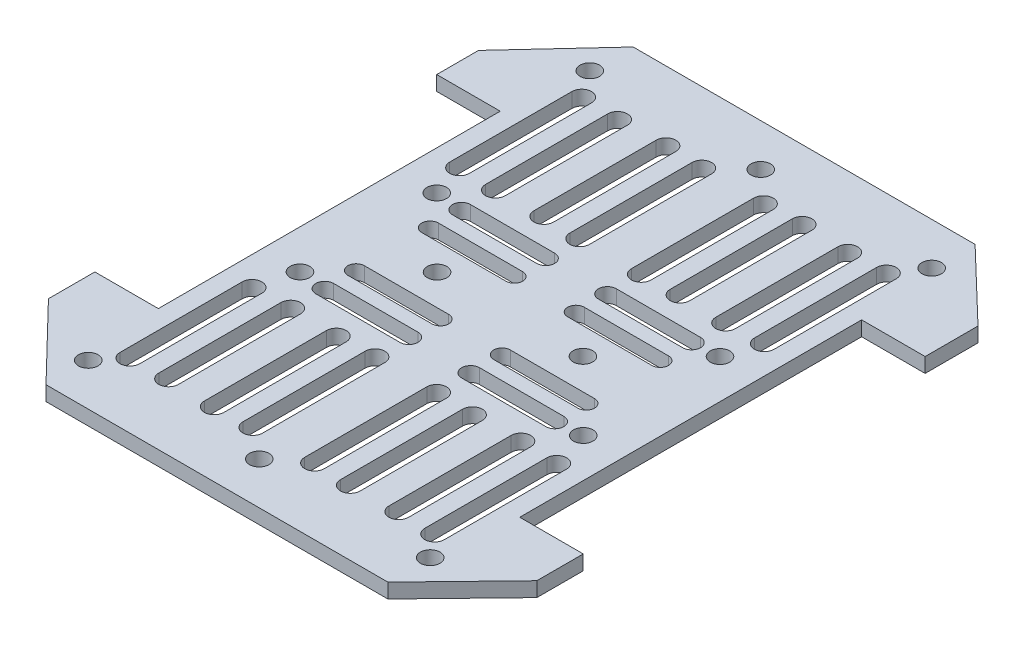
SolidWorks part; units mm, degrees
ref_plane "Front Plane" through (0, 0, 0) normal (0, 0, 1) x (1, 0, 0)
ref_plane "Top Plane" through (0, 0, 0) normal (0, 1, 0) x (1, 0, 0)
ref_plane "Right Plane" through (0, 0, 0) normal (1, 0, 0) x (0, 0, -1)
sketch "Sketch1" plane through (0, 0, 0) normal (0, 1, 0) x (1, 0, 0)
  line L0 (-79.583, 48.3629) -> (-79.583, 23.3559)
  line L1 (-83.6071, 48.3629) -> (-83.6071, 23.3559)
  line L2 (-71.9541, 48.0755) -> (-71.9541, 23.0685)
  line L3 (-73.9662, 14.2814) -> (-91.2181, 14.2814)
  line L4 (-75.9782, 48.0755) -> (-75.9782, 23.0685)
  line L5 (-96.8349, 48.3629) -> (-96.8349, 23.3559)
  line L6 (-100.859, 48.3629) -> (-100.859, 23.3559)
  line L7 (-89.206, 48.0755) -> (-89.206, 23.0685)
  line L8 (-93.2301, 48.0755) -> (-93.2301, 23.0685)
  line L9 (-55.7275, 48.3629) -> (-55.7275, 23.3559)
  line L10 (-51.7033, 48.3629) -> (-51.7033, 23.3559)
  line L11 (-63.3564, 48.0755) -> (-63.3564, 23.0685)
  line L12 (-59.3322, 48.0755) -> (-59.3322, 23.0685)
  line L13 (-38.4756, 48.3629) -> (-38.4756, 23.3559)
  line L14 (-34.4515, 48.3629) -> (-34.4515, 23.3559)
  line L15 (-46.1045, 48.0755) -> (-46.1045, 23.0685)
  line L16 (-42.0804, 48.0755) -> (-42.0804, 23.0685)
  line L17 (-117.7082, 46.1857) -> (-117.7082, 37.5391)
  line L18 (-79.583, -44.139) -> (-79.583, -19.132)
  line L19 (-83.6071, -44.139) -> (-83.6071, -19.132)
  line L20 (-71.9541, -43.8516) -> (-71.9541, -18.8446)
  line L21 (-75.9782, -43.8516) -> (-75.9782, -18.8446)
  line L22 (-96.8349, -44.139) -> (-96.8349, -19.132)
  line L23 (-100.859, -44.139) -> (-100.859, -19.132)
  line L24 (-89.206, -43.8516) -> (-89.206, -18.8446)
  line L25 (-93.2301, -43.8516) -> (-93.2301, -18.8446)
  line L26 (-55.7275, -44.139) -> (-55.7275, -19.132)
  line L27 (-51.7033, -44.139) -> (-51.7033, -19.132)
  line L28 (-63.3564, -43.8516) -> (-63.3564, -18.8446)
  line L29 (-59.3322, -43.8516) -> (-59.3322, -18.8446)
  line L30 (-32.7082, -57.4609) -> (-102.7082, -57.4609)
  line L31 (-117.7082, 46.1857) -> (-117.6732, 46.1313)
  line L32 (-32.4828, 62.5391) -> (-102.4828, 62.5391)
  line L33 (-102.4828, 62.5391) -> (-117.6732, 46.1313)
  line L34 (-102.7082, -57.4609) -> (-117.7082, -41.9617)
  line L36 (-117.7082, 37.5391) -> (-104.7082, 37.5391)
  line L37 (-117.7082, -32.4609) -> (-104.7082, -32.4609)
  line L38 (-104.7082, 37.5391) -> (-104.7082, -32.4609)
  line L39 (-38.4756, -44.139) -> (-38.4756, -19.132)
  line L40 (-117.7082, -32.4609) -> (-117.7082, -41.9617)
  line L41 (-34.4515, -44.139) -> (-34.4515, -19.132)
  line L42 (-46.1045, -43.8516) -> (-46.1045, -18.8446)
  line L43 (-42.0804, -43.8516) -> (-42.0804, -18.8446)
  line L44 (-73.9662, 17.9425) -> (-91.2181, 17.9425)
  line L45 (-73.9662, 7.9844) -> (-91.2181, 7.9844)
  line L46 (-73.9662, 11.3858) -> (-91.2181, 11.3858)
  line L47 (-61.3443, 14.2814) -> (-44.0924, 14.2814)
  line L48 (-61.3443, 17.9425) -> (-44.0924, 17.9425)
  line L49 (-61.3443, 7.9844) -> (-44.0924, 7.9844)
  line L50 (-61.3443, 11.3858) -> (-44.0924, 11.3858)
  line L51 (-73.9662, -10.0575) -> (-91.2181, -10.0575)
  line L52 (-73.9662, -13.7186) -> (-91.2181, -13.7186)
  line L53 (-73.9662, -3.7605) -> (-91.2181, -3.7605)
  line L54 (-73.9662, -7.1619) -> (-91.2181, -7.1619)
  line L55 (-61.3443, -10.0575) -> (-44.0924, -10.0575)
  line L56 (-61.3443, -13.7186) -> (-44.0924, -13.7186)
  line L57 (-61.3443, -3.7605) -> (-44.0924, -3.7605)
  line L58 (-61.3443, -7.1619) -> (-44.0924, -7.1619)
  line L59 (-32.7082, -57.4609) -> (-17.7082, -41.9617)
  line L60 (-32.4828, 62.5391) -> (-17.7082, 48.3629)
  line L61 (-30.7082, 37.5391) -> (-30.7082, -32.4609)
  line L62 (-17.7082, -32.4609) -> (-30.7082, -32.4609)
  line L63 (-17.7082, 37.5391) -> (-30.7082, 37.5391)
  line L64 (-17.7082, -41.9617) -> (-17.7082, -32.4609)
  line L65 (-17.7082, 37.5391) -> (-17.7082, 48.3629)
  circle A0 centre (-96.7082, 16.5391) radius 2
  circle A1 centre (-96.7082, -11.4609) radius 2
  circle A2 centre (-102.7082, -48.8007) radius 2
  circle A3 centre (-67.7082, -48.8007) radius 2
  arc A4 (-79.583, 23.3559) -> (-83.6071, 23.3559) centre (-81.5951, 23.3559) cw
  arc A5 (-83.6071, 48.3629) -> (-79.583, 48.3629) centre (-81.5951, 48.3629) cw
  arc A6 (-71.9541, 23.0685) -> (-75.9782, 23.0685) centre (-73.9662, 23.0685) cw
  arc A7 (-75.9782, 48.0755) -> (-71.9541, 48.0755) centre (-73.9662, 48.0755) cw
  arc A8 (-96.8349, 23.3559) -> (-100.859, 23.3559) centre (-98.847, 23.3559) cw
  arc A9 (-100.859, 48.3629) -> (-96.8349, 48.3629) centre (-98.847, 48.3629) cw
  arc A10 (-89.206, 23.0685) -> (-93.2301, 23.0685) centre (-91.2181, 23.0685) cw
  arc A11 (-93.2301, 48.0755) -> (-89.206, 48.0755) centre (-91.2181, 48.0755) cw
  arc A12 (-55.7275, 23.3559) -> (-51.7033, 23.3559) centre (-53.7154, 23.3559) ccw
  arc A13 (-51.7033, 48.3629) -> (-55.7275, 48.3629) centre (-53.7154, 48.3629) ccw
  arc A14 (-63.3564, 23.0685) -> (-59.3322, 23.0685) centre (-61.3443, 23.0685) ccw
  arc A15 (-59.3322, 48.0755) -> (-63.3564, 48.0755) centre (-61.3443, 48.0755) ccw
  arc A16 (-38.4756, 23.3559) -> (-34.4515, 23.3559) centre (-36.4635, 23.3559) ccw
  arc A17 (-34.4515, 48.3629) -> (-38.4756, 48.3629) centre (-36.4635, 48.3629) ccw
  arc A18 (-46.1045, 23.0685) -> (-42.0804, 23.0685) centre (-44.0924, 23.0685) ccw
  arc A19 (-42.0804, 48.0755) -> (-46.1045, 48.0755) centre (-44.0924, 48.0755) ccw
  arc A20 (-79.583, -19.132) -> (-83.6071, -19.132) centre (-81.5951, -19.132) ccw
  arc A21 (-83.6071, -44.139) -> (-79.583, -44.139) centre (-81.5951, -44.139) ccw
  arc A22 (-71.9541, -18.8446) -> (-75.9782, -18.8446) centre (-73.9662, -18.8446) ccw
  arc A23 (-75.9782, -43.8516) -> (-71.9541, -43.8516) centre (-73.9662, -43.8516) ccw
  arc A24 (-96.8349, -19.132) -> (-100.859, -19.132) centre (-98.847, -19.132) ccw
  arc A25 (-100.859, -44.139) -> (-96.8349, -44.139) centre (-98.847, -44.139) ccw
  arc A26 (-89.206, -18.8446) -> (-93.2301, -18.8446) centre (-91.2181, -18.8446) ccw
  arc A27 (-93.2301, -43.8516) -> (-89.206, -43.8516) centre (-91.2181, -43.8516) ccw
  circle A28 centre (-102.7082, 53.8788) radius 2
  circle A29 centre (-67.7082, 53.8788) radius 2
  arc A30 (-55.7275, -19.132) -> (-51.7033, -19.132) centre (-53.7154, -19.132) cw
  arc A31 (-51.7033, -44.139) -> (-55.7275, -44.139) centre (-53.7154, -44.139) cw
  arc A32 (-63.3564, -18.8446) -> (-59.3322, -18.8446) centre (-61.3443, -18.8446) cw
  arc A33 (-59.3322, -43.8516) -> (-63.3564, -43.8516) centre (-61.3443, -43.8516) cw
  arc A34 (-38.4756, -19.132) -> (-34.4515, -19.132) centre (-36.4635, -19.132) cw
  arc A35 (-34.4515, -44.139) -> (-38.4756, -44.139) centre (-36.4635, -44.139) cw
  arc A36 (-46.1045, -18.8446) -> (-42.0804, -18.8446) centre (-44.0924, -18.8446) cw
  arc A37 (-42.0804, -43.8516) -> (-46.1045, -43.8516) centre (-44.0924, -43.8516) cw
  arc A38 (-91.2181, 14.2814) -> (-91.2181, 17.9425) centre (-91.2181, 16.112) cw
  arc A39 (-73.9662, 17.9425) -> (-73.9662, 14.2814) centre (-73.9662, 16.112) cw
  arc A40 (-91.2181, 7.9844) -> (-91.2181, 11.3858) centre (-91.2181, 9.6851) cw
  arc A41 (-73.9662, 11.3858) -> (-73.9662, 7.9844) centre (-73.9662, 9.6851) cw
  arc A42 (-44.0924, 14.2814) -> (-44.0924, 17.9425) centre (-44.0924, 16.112) ccw
  arc A43 (-61.3443, 17.9425) -> (-61.3443, 14.2814) centre (-61.3443, 16.112) ccw
  arc A44 (-44.0924, 7.9844) -> (-44.0924, 11.3858) centre (-44.0924, 9.6851) ccw
  arc A45 (-61.3443, 11.3858) -> (-61.3443, 7.9844) centre (-61.3443, 9.6851) ccw
  arc A46 (-91.2181, -10.0575) -> (-91.2181, -13.7186) centre (-91.2181, -11.888) ccw
  arc A47 (-73.9662, -13.7186) -> (-73.9662, -10.0575) centre (-73.9662, -11.888) ccw
  arc A48 (-91.2181, -3.7605) -> (-91.2181, -7.1619) centre (-91.2181, -5.4612) ccw
  arc A49 (-73.9662, -7.1619) -> (-73.9662, -3.7605) centre (-73.9662, -5.4612) ccw
  arc A50 (-44.0924, -10.0575) -> (-44.0924, -13.7186) centre (-44.0924, -11.888) cw
  arc A51 (-61.3443, -13.7186) -> (-61.3443, -10.0575) centre (-61.3443, -11.888) cw
  arc A52 (-44.0924, -3.7605) -> (-44.0924, -7.1619) centre (-44.0924, -5.4612) cw
  arc A53 (-61.3443, -7.1619) -> (-61.3443, -3.7605) centre (-61.3443, -5.4612) cw
  circle A54 centre (-32.7082, 53.8788) radius 2
  circle A55 centre (-32.7082, -48.8007) radius 2
  circle A56 centre (-38.7082, -11.4609) radius 2
  circle A57 centre (-38.7082, 16.5391) radius 2
  circle A58 centre (-52.7714, 2.5391) radius 2
  circle A59 centre (-82.6451, 2.5391) radius 2
  dimension "D2" = 4
  dimension "D3" = 4
  dimension "D4" = 4
  dimension "D5" = 4
  dimension "D1" = 13
extrude "Boss-Extrude1" add sketch "Sketch1" along normal blind 3
